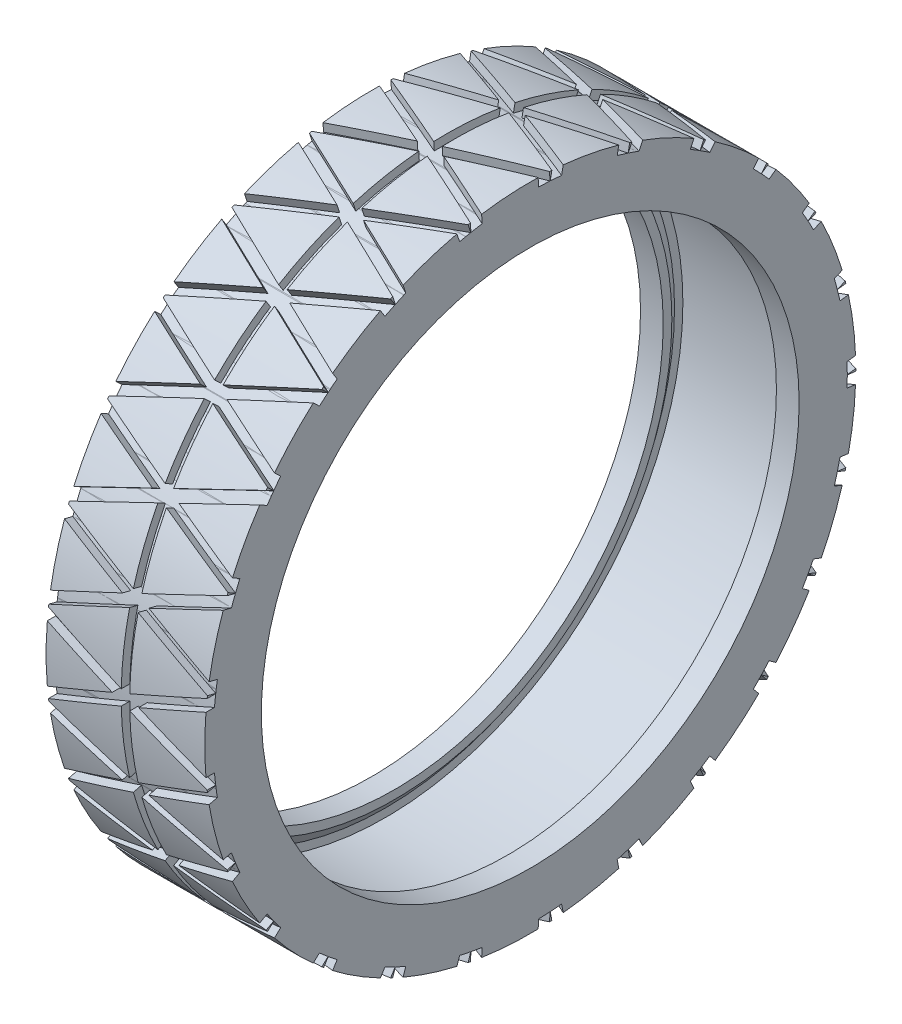
SolidWorks part; units mm, degrees
ref_plane "Front Plane" through (0, 0, 0) normal (0, 0, 1) x (1, 0, 0)
ref_plane "Top Plane" through (0, 0, 0) normal (0, 1, 0) x (1, 0, 0)
ref_plane "Right Plane" through (0, 0, 0) normal (1, 0, 0) x (0, 0, -1)
sketch "Sketch1" plane through (0, 0, 0) normal (0, 0, 1) x (1, 0, 0)
  line L0 (0, 115) -> (28.02, 115)
  line L1 (28.02, 115) -> (28.02, 95)
  line L2 (28.02, 95) -> (20, 95)
  line L3 (20, 95) -> (20, 98.05)
  line L6 (23.1, 105.05) -> (0, 105.05)
  line L7 (0, 105.05) -> (0, 115)
  line L8 (23.1, 105.05) -> (23.1, 102.1)
  line L9 (23.1, 102.1) -> (20, 98.05)
  point P9 (11.2578, 117.0242)
  dimension "D1" = 105.05
  dimension "D2" = 115
  dimension "D3" = 23.1
  dimension "D4" = 4.92
  dimension "D5" = 98.05
  dimension "D7" = 3.1
  dimension "D8" = 4.05
  dimension "D9" = 20
ref_axis "Axis1" through (26.25, 0, 0) along (-1, 0, 0)
revolve "Revolve1" add sketch "Sketch1" angle 360 about axis through (26.25, 0, 0) along (-1, 0, 0)
mirror "Mirror1" about plane through (0, 105.05, 0) normal (-1, 0, 0) of "Revolve1"
sketch "Sketch2" plane through (0, 0, 0) normal (0, 1, 0) x (1, 0, 0)
  line L2 (-28.02, 115) -> (-28.02, -115) construction
  line L3 (-28.02, 112) -> (28.02, 112)
  line L4 (28.02, -115) -> (28.02, 115) construction
  dimension "D1" = 112
surface "Surface-Revolve1" sketch "Sketch2" parameters "D1"=360
ref_plane "Plane1" through (0, 0, 116) normal (0, 0, 1) x (1, 0, 0)
sketch "Sketch3" plane through (0, 0, 116) normal (0, 0, 1) x (1, 0, 0)
  line L0 (-28.02, 14) -> (0, 2)
  line L1 (-28.02, 95) -> (-28.02, -95) construction
  line L2 (28.02, -115) -> (28.02, 115) construction
  line L3 (28.02, -10) -> (28.02, -14)
  line L4 (28.02, -14) -> (0, -2)
  line L5 (-28.02, -14) -> (0, -2)
  line L6 (28.02, 10) -> (28.02, 14)
  line L7 (28.02, 14) -> (0, 2)
  line L8 (-28.02, -10) -> (-28.02, -14)
  line L9 (-4.67, 0) -> (-28.02, 10)
  line L10 (-28.02, 10) -> (-28.02, 14)
  line L11 (4.67, 0) -> (28.02, -10)
  line L12 (-4.67, 0) -> (-28.02, -10)
  line L13 (4.67, 0) -> (28.02, 10)
  point P12 (0, 0)
  point P13 (0, 0)
  dimension "D1" = 4
  dimension "D2" = 4
  dimension "D3" = 4
  dimension "D4" = 20
  dimension "D5" = 20
  dimension "D6" = 10
  dimension "D7" = 10
extrude "Cut-Extrude1" cut sketch "Sketch3" against normal up to surface (4.4473 mm away)
pattern_circular "CirPattern1" count 25 over 360 about axis through (0, 0, 0) along (1, 0, 0) of "Cut-Extrude1"
sketch "Sketch4" plane through (0, 0, 0) normal (0, 0, 1) x (1, 0, 0)
  line L0 (1.5, 115) -> (-1.5, 115)
  line L6 (-1.5, 115) -> (-1.5, 112)
  line L7 (-1.5, 112) -> (1.5, 112)
  line L8 (1.5, 112) -> (1.5, 115)
  point P4 (0, 112)
  dimension "D1" = 115
  dimension "D2" = 3
  dimension "D3" = 3
revolve "Cut-Revolve1" cut sketch "Sketch4" angle 360 about axis through (26.25, 0, 0) along (-1, 0, 0)
